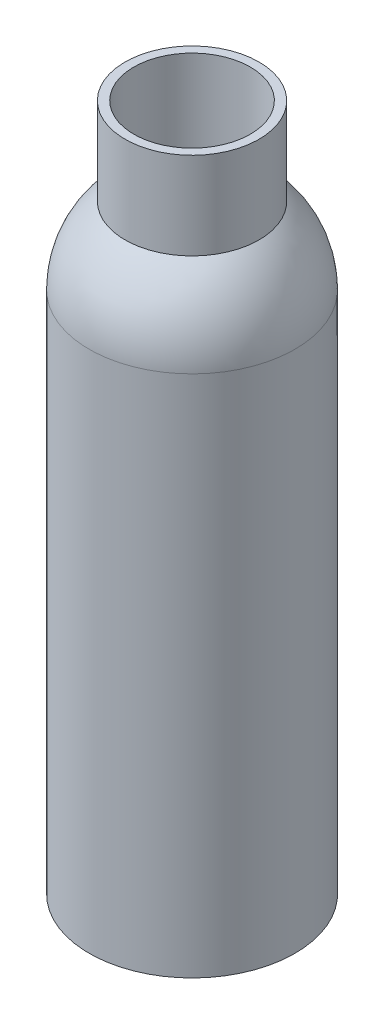
SolidWorks part; units mm, degrees
material "AISI 316 Stainless Steel Sheet (SS)"
ref_plane "Front Plane" through (0, 0, 0) normal (0, 0, 1) x (1, 0, 0)
ref_plane "Top Plane" through (0, 0, 0) normal (0, 1, 0) x (1, 0, 0)
ref_plane "Right Plane" through (0, 0, 0) normal (1, 0, 0) x (0, 0, -1)
sketch "Sketch3" plane through (0, 0, 0) normal (0, 0, 1) x (1, 0, 0)
  line L0 (0, 0) -> (37.465, 0)
  line L1 (37.465, 0) -> (37.465, 190.5)
  line L3 (24.384, 218.44) -> (24.384, 250.19)
  line L4 (24.384, 250.19) -> (21.209, 250.19)
  line L5 (0, 3.175) -> (0, 0)
  line L6 (0, 3.175) -> (34.925, 3.175)
  line L7 (34.925, 3.175) -> (34.925, 187.5773)
  line L9 (21.209, 218.44) -> (21.209, 250.19)
  line L10 (0, 0) -> (0, 387.2752) construction
  arc A0 (24.384, 218.44) -> (37.465, 190.5) centre (1.0857, 190.5) cw
  arc A1 (21.209, 218.44) -> (34.925, 187.5773) centre (-6.6554, 187.5773) cw
  dimension "D1" = 37.465
  dimension "D2" = 34.925
  dimension "D3" = 3.175
  dimension "D4" = 24.384
  dimension "D5" = 3.175
  dimension "D6" = 250.19
  dimension "D7" = 218.44
  dimension "D8" = 190.5
revolve "Revolve1" add sketch "Sketch3" angle 360 about L10
